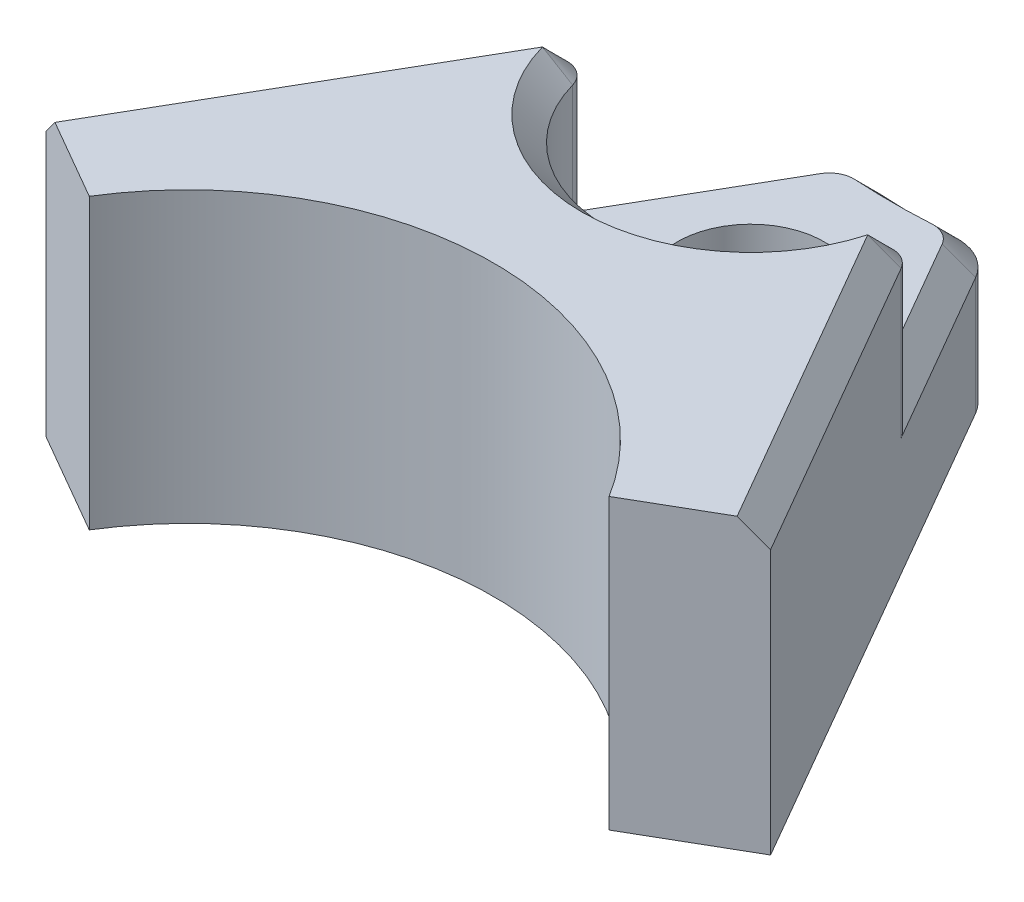
SolidWorks part; units mm, degrees
ref_plane "Front Plane" through (0, 0, 0) normal (0, 0, 1) x (1, 0, 0)
ref_plane "Top Plane" through (0, 0, 0) normal (0, 1, 0) x (1, 0, 0)
ref_plane "Right Plane" through (0, 0, 0) normal (1, 0, 0) x (0, 0, -1)
sketch "Sketch1" plane through (0, 0, 0) normal (0, 1, 0) x (1, 0, 0)
  line L0 (0, 10.1897) -> (0, -1.7012) construction
  line L1 (-11.8909, 3.3) -> (11.5401, 3.3) construction
  line L2 (-26.2996, 17.32) -> (19.7259, 17.32) construction
  line L3 (0, 17.32) -> (13.353, -5.808) construction
  line L4 (5.3078, 3.3) -> (7.3978, 4.5067)
  line L5 (-34.4424, 27.39) -> (17.8409, 27.39) construction
  line L6 (7.3978, 4.5067) -> (1.3601, 14.9642)
  line L7 (-7.3978, 4.5067) -> (-1.3601, 14.9642)
  line L8 (-5.3078, 3.3) -> (-7.3978, 4.5067)
  circle A0 centre (0, 0) radius 6.25 construction
  circle A1 centre (0, 11.5) radius 1.5
  arc A2 (-5.3078, 3.3) -> (5.3078, 3.3) centre (0, 0) cw
  circle A3 centre (0, 27.39) radius 12.5 construction
  arc A4 (-1.3601, 14.9642) -> (1.3601, 14.9642) centre (0, 27.39) ccw
  point P15 (0, 17.32)
  dimension "D1" = 12.5
  dimension "D2" = 3
  dimension "D3" = 11.5
  dimension "D9" = 25
  dimension "D4" = 3.3
  dimension "D5" = 17.32
  dimension "D6" = 30
  dimension "D7" = 60
  dimension "D8" = 27.39
extrude "Base" add sketch "Sketch1" along normal blind 5.9
sketch "Sketch2" plane through (0, 5.9, 0) normal (0, 1, 0) x (1, 0, 0)
  line L0 (-1.3601, 14.9642) -> (-7.3978, 4.5067) construction
  line L1 (7.3978, 4.5067) -> (1.3601, 14.9642) construction
  line L2 (-2.7622, 12.5357) -> (-1.3601, 14.9642)
  line L3 (2.7622, 12.5357) -> (1.3601, 14.9642)
  circle A0 centre (0, 11.5) radius 2.95 construction
  arc A1 (-2.7622, 12.5357) -> (2.7622, 12.5357) centre (0, 11.5) ccw
  arc A2 (-1.3601, 14.9642) -> (1.3601, 14.9642) centre (0, 27.39) ccw
  arc A3 (-1.3601, 14.9642) -> (1.3601, 14.9642) centre (0, 27.39) ccw construction
  dimension "D1" = 5.9
extrude "Fastener Clearance" cut sketch "Sketch2" against normal blind 3
fillet "Fastener Fillet" radius 0.5 2 edges at (2.7622, 4.4, -12.5357) (-2.7622, 4.4, -12.5357)
fillet "Base Fillet" radius 1 2 edges at (-1.3601, 1.45, -14.9642) (1.3601, 1.45, -14.9642)
chamfer "Body Chamfer" distance 0.5 angle 45 10 edges at (-2.716, 2.9, -12.6157) (-1.2852, 2.9, -14.7951) (0, 2.9, -14.89) (1.2852, 2.9, -14.7951) (2.716, 2.9, -12.6157) (-5.5761, 5.9, -7.6619) (-3.2592, 5.9, -11.0632) (0, 5.9, -8.55) (3.2592, 5.9, -11.0632) (5.5761, 5.9, -7.6619)
